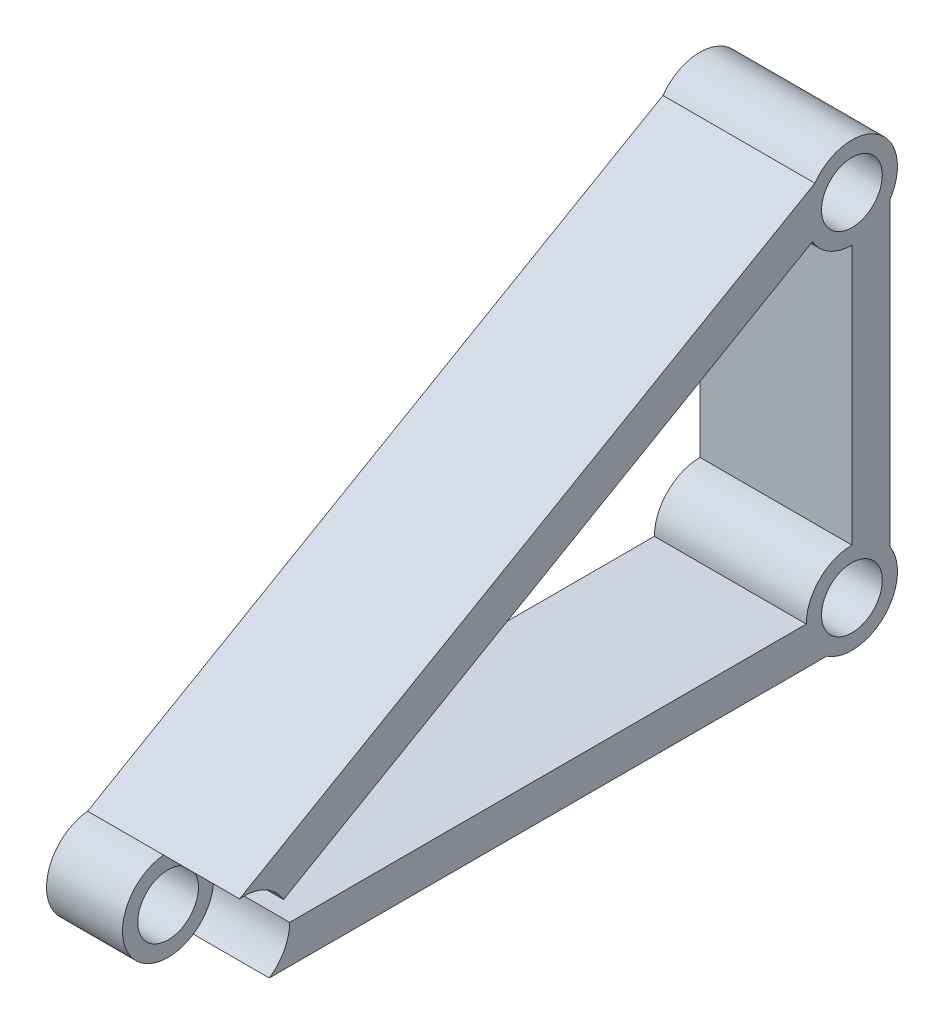
SolidWorks part; units mm, degrees
material "Thornel Mat VMA"
ref_plane "Front Plane" through (0, 0, 0) normal (0, 0, 1) x (1, 0, 0)
ref_plane "Top Plane" through (0, 0, 0) normal (0, 1, 0) x (1, 0, 0)
ref_plane "Right Plane" through (0, 0, 0) normal (1, 0, 0) x (0, 0, -1)
sketch "Sketch2" plane through (0, 0, 0) normal (1, 0, 0) x (0, 0, -1)
  line L0 (1528.6955, 519.1525) -> (1528.6955, 177.2722)
  line L2 (1476.734, 549.1525) -> (780.657, 147.2722)
  line L3 (722.7516, 176.9771) -> (1479.9615, 614.1525)
  line L4 (761.8617, 67.2722) -> (1495.5292, 67.2722)
  line L5 (1578.6955, 545.9862) -> (1578.6955, 150.4385)
  line L6 (1468.6955, 117.2722) -> (788.6955, 117.2722)
  line L7 (780.657, 147.2722) -> (728.6955, 117.2722) construction
  line L8 (728.6955, 117.2722) -> (788.6955, 117.2722) construction
  line L9 (1528.6955, 177.2722) -> (1528.6955, 117.2722) construction
  line L10 (1528.6955, 117.2722) -> (1468.6955, 117.2722) construction
  line L11 (1476.734, 549.1525) -> (1528.6955, 579.1525) construction
  line L12 (1528.6955, 579.1525) -> (1528.6955, 519.1525) construction
  line L13 (1479.9615, 614.1525) -> (1502.7147, 564.1525) construction
  arc A0 (780.657, 147.2722) -> (788.6955, 117.2722) centre (728.6955, 117.2722) ccw
  arc A1 (1528.6955, 519.1525) -> (1476.734, 549.1525) centre (1528.6955, 579.1525) ccw
  arc A2 (1468.6955, 117.2722) -> (1528.6955, 177.2722) centre (1528.6955, 117.2722) ccw
  circle A3 centre (728.6955, 117.2722) radius 40
  circle A4 centre (1528.6955, 579.1525) radius 40
  circle A5 centre (1528.6955, 117.2722) radius 40
  arc A6 (788.6955, 117.2722) -> (780.657, 147.2722) centre (728.6955, 117.2722) ccw
  arc A7 (1468.6955, 117.2722) -> (1528.6955, 177.2722) centre (1528.6955, 117.2722) cw
  arc A8 (1476.734, 549.1525) -> (1528.6955, 519.1525) centre (1528.6955, 579.1525) ccw
  dimension "D3" = 120
  dimension "D7" = 80
  dimension "D2" = 800
  dimension "D1" = 90
  dimension "D5" = 30
  dimension "D6" = 50
  dimension "D8" = 50
  dimension "D4" = 50
extrude "Boss-Extrude1" add sketch "Sketch2" along normal blind 200 contours A2 L6 A0 L4 | A1 L3 A0 L2 | A2 L5 A1 L0 | A0 A6 A3 | A7 A2 A5 | A1 A8 A4
sketch "Sketch4" plane through (0, 0, 0) normal (1, 0, 0) x (0, 0, -1)
  circle A0 centre (728.6955, 117.2722) radius 60
  dimension "D1" = 120
extrude "Cut-Extrude1" cut sketch "Sketch4" against normal blind 100 from surface at 200 starting at face at (200, 272.2313, -1259.617)
equation "\"controlAngle\"= 30deg"
equation "\"baseLength\"= 80cm"
equation "\"D2@Sketch2\"=\"baseLength\""
equation "\"D3@Sketch2\"=1.5*\"HoleMountDiameter@PrintingPress.Assembly\""
equation "\"D7@Sketch2\"=\"HoleMountDiameter@PrintingPress.Assembly\""
equation "\"D5@Sketch2\"=\"controlAngle\""
equation "\"D8@Sketch2\"=0.5*\"RivetLength@PrintingPress.Assembly\""
equation "\"D4@Sketch2\"=0.5*\"RivetLength@PrintingPress.Assembly\""
equation "\"D1@Boss-Extrude1\"=2*\"RivetLength@PrintingPress.Assembly\""
equation "\"D1@Sketch4\"=1.5*\"HoleMountDiameter@PrintingPress.Assembly\""
equation "\"D1@Cut-Extrude1\"=\"RivetLength@PrintingPress.Assembly\""
